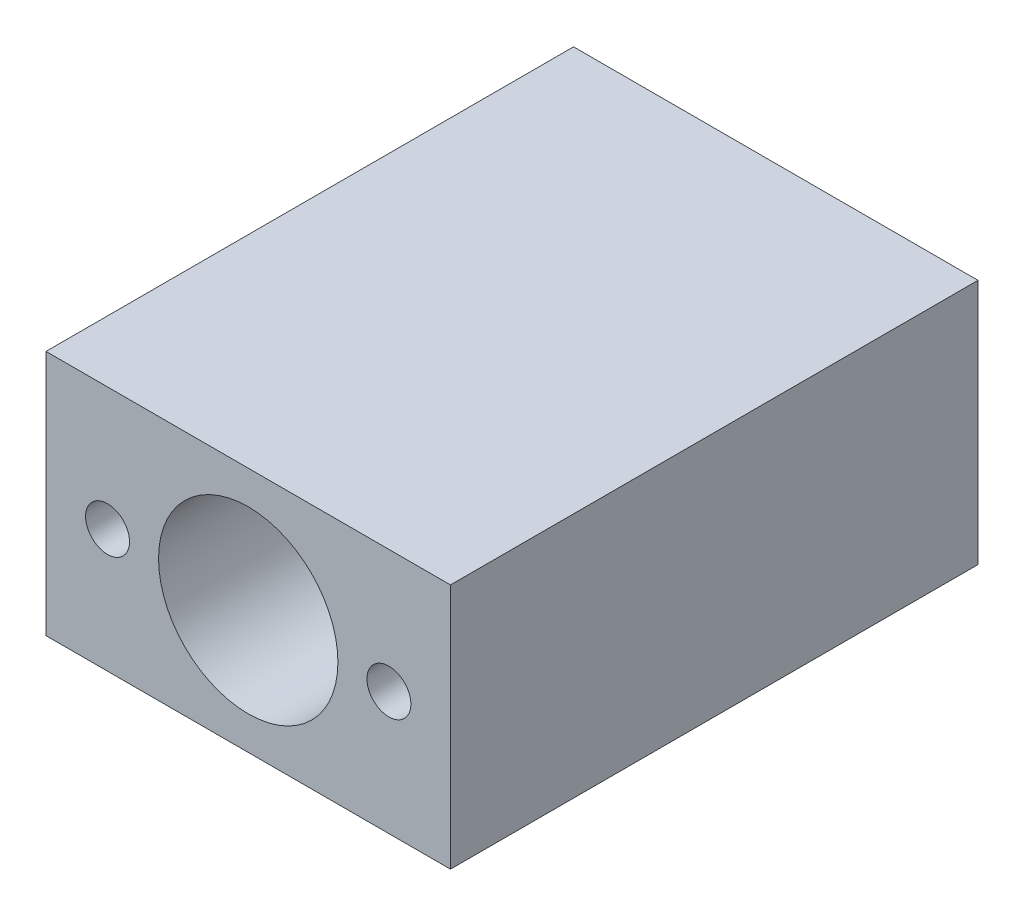
SolidWorks part; units mm, degrees
ref_plane "Alzado" through (0, 0, 0) normal (0, 0, 1) x (1, 0, 0)
ref_plane "Planta" through (0, 0, 0) normal (0, 1, 0) x (1, 0, 0)
ref_plane "Vista lateral" through (0, 0, 0) normal (1, 0, 0) x (0, 0, -1)
sketch "Croquis1" plane through (0, 0, 0) normal (0, 0, 1) x (1, 0, 0)
  line L1 (0, 0) -> (23, 0)
  line L2 (0, 0) -> (0, 14)
  line L3 (0, 14) -> (23, 14)
  line L4 (23, 0) -> (23, 14)
  circle A0 centre (11.5, 7) radius 5.1
  dimension "D9" = 10.2
  dimension "D1" = 14
  dimension "D2" = 23
  dimension "D3" = 11.5
  dimension "D4" = 7
extrude "Saliente-Extruir1" add sketch "Croquis1" along normal blind 30
hole_wizard "Perforador para roscar para macho de roscar para M31" positions "Croquis2" profile "Croquis3" hole size "M3" standard "DIN"
sketch "Croquis2" plane through (0, 0, 30) normal (0, 0, 1) x (1, 0, 0)
  line L0 (0, 0) -> (23, 0) construction
  circle A0 centre (11.5, 7) radius 5.1 construction
  point P0 (3.5, 7)
  point P2 (19.5, 7)
  dimension "D1" = 8
  dimension "D2" = 8
  dimension "D3" = 7
  dimension "D4" = 7
sketch "Croquis3" plane through (3.5, 7, 30) normal (1, 0, 0) x (0, -1, 0)
  line L0 (0, 0) -> (0, 12.7511)
  line L1 (0, 12.7511) -> (1.25, 12)
  line L2 (1.25, 12) -> (1.25, 0)
  line L5 (1.25, 0) -> (0, 0)
  line L10 (0, 12.7511) -> (-1.25, 12) construction
  line L11 (0, -6.35) -> (0, 107.95) construction
  dimension "Diámetro de taladro" = 2.5
  dimension "Profundidad de taladro" = 12
  dimension "Ángulo de perforador" = 118
